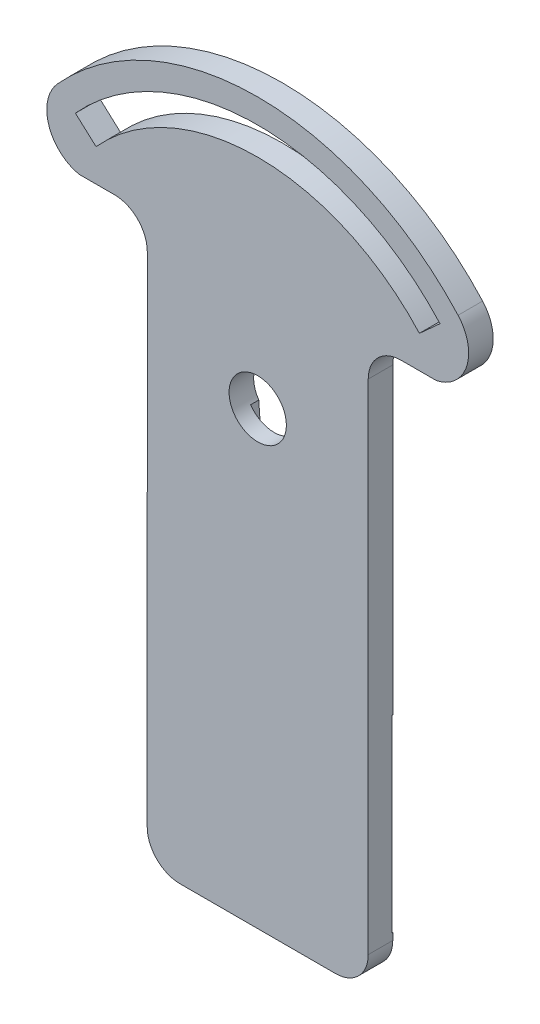
SolidWorks part; units mm, degrees
ref_plane "Alzado" through (0, 0, 0) normal (0, 0, 1) x (1, 0, 0)
ref_plane "Planta" through (0, 0, 0) normal (0, 1, 0) x (1, 0, 0)
ref_plane "Vista lateral" through (0, 0, 0) normal (1, 0, 0) x (0, 0, -1)
sketch "Corte exterior" plane through (0, 0, 0) normal (0, 0, 1) x (1, 0, 0)
  line L0 (39.5043, -30.6861) -> (20.5043, -30.6861)
  line L1 (12.511, 38.2118) -> (8.1613, 38.2118)
  line L2 (16.5043, -26.6861) -> (16.511, 34.2118)
  line L3 (43.5043, 34.2118) -> (43.5043, -26.6861)
  line L4 (16.5043, -26.6861) -> (16.511, 34.2118)
  line L5 (10.2531, 42.1758) -> (7.7314, 44.4563)
  line L6 (52.2773, 44.4563) -> (49.7555, 42.1758)
  line L7 (47.5043, 38.2118) -> (51.8473, 38.2118)
  arc A0 (16.511, 34.2118) -> (12.511, 38.2118) centre (12.511, 34.2118) ccw
  arc A1 (47.5043, 38.2118) -> (43.5043, 34.2118) centre (47.5043, 34.2118) ccw
  arc A2 (39.5043, -30.6861) -> (43.5043, -26.6861) centre (39.5043, -26.6861) ccw
  arc A3 (16.5043, -26.6861) -> (20.5043, -30.6861) centre (20.5043, -26.6861) ccw
  arc A4 (49.7555, 42.1758) -> (10.2531, 42.1758) centre (30.0043, 24.3139) ccw
  arc A5 (52.2773, 44.4563) -> (7.7314, 44.4563) centre (30.0043, 24.3139) ccw
  circle A6 centre (30.0043, 24.3139) radius 3.5
  arc A7 (54.4801, 46.4484) -> (5.5286, 46.4484) centre (30.0043, 24.3139) ccw
  arc A8 (5.5286, 46.4484) -> (8.1613, 38.2118) centre (9.237, 43.0947) ccw
  arc A9 (51.8473, 38.2118) -> (54.4801, 46.4484) centre (50.7716, 43.0947) ccw
sketch "Grabado Superficie" plane through (0, 0, 0) normal (0, 0, 1) x (1, 0, 0)
  line L0 (32.8737, 22.3097) -> (31.9994, 9.9231)
  line L1 (28.0093, 9.9231) -> (27.135, 22.3097)
  arc A0 (28.0093, 9.9231) -> (31.9994, 9.9231) centre (30.0043, 10.0639) ccw
  arc A1 (27.135, 22.3097) -> (32.8737, 22.3097) centre (30.0043, 24.3139) ccw
sketch "grabado linea medio" plane through (0, 0, 0) normal (0, 0, 1) x (1, 0, 0)
  line L0 (16.5043, -26.0461) -> (24.6443, -26.0461)
  line L1 (24.6443, -26.0461) -> (24.6443, -30.6861)
  line L2 (27.1643, -30.6861) -> (27.1643, -26.0449)
  line L3 (27.1643, -26.0449) -> (43.5043, -25.8449)
  line L4 (43.5043, -2.8161) -> (27.1643, -2.8161)
  line L5 (27.1643, -2.8161) -> (27.1643, 1.8239)
  line L6 (27.1643, 1.8239) -> (24.6443, 1.8239)
  line L7 (24.6443, 1.8239) -> (24.6443, -2.8161)
  line L8 (24.6443, -2.8161) -> (20.5843, -2.8161)
  line L9 (20.5843, -2.8161) -> (20.5843, -10.8961)
  line L10 (20.5843, -10.8961) -> (16.5043, -10.8961)
  line L11 (16.5043, -10.8961) -> (16.5043, -26.0461)
  line L12 (24.6443, -30.6861) -> (27.1643, -30.6861)
  line L13 (43.5043, -2.8161) -> (43.5043, -25.8449)
extrude "Saliente-Extruir1" add sketch "Corte exterior" along normal blind 3 contours L7 A9 A7 A8 L1 A0 L2 A3 L0 A2 L3 A1 A5 L6 A4 L5 A6
extrude "Cortar-Extruir1" cut sketch "Grabado Superficie" along normal blind 1
extrude "Cortar-Extruir2" cut sketch "grabado linea medio" along normal blind 0.1
